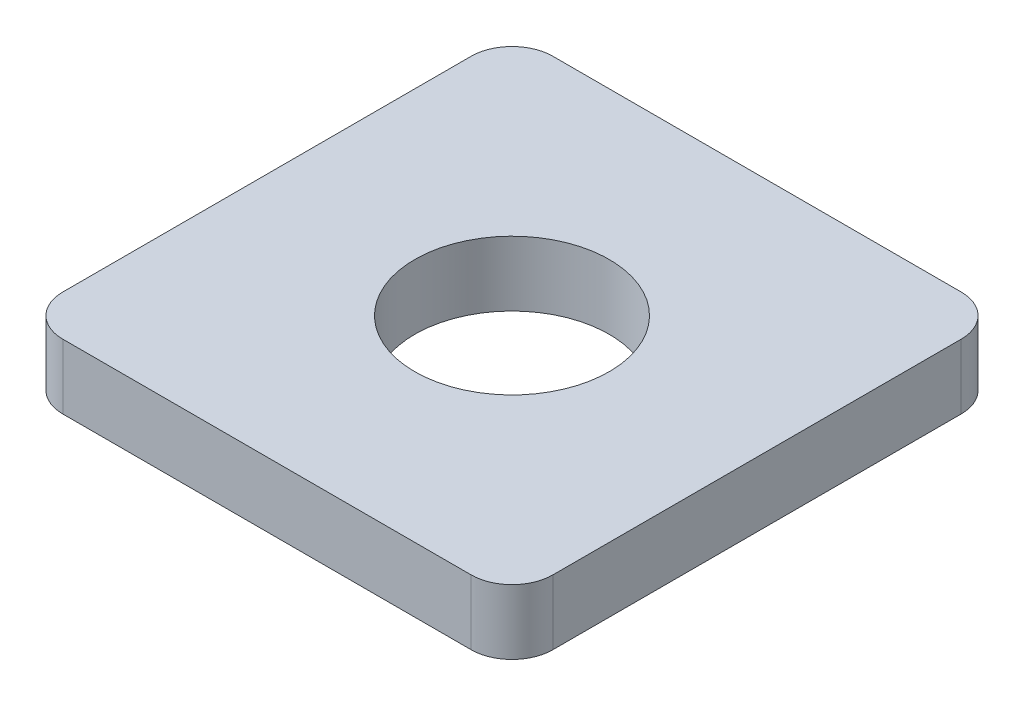
SolidWorks part; units mm, degrees
ref_plane "Front Plane" through (0, 0, 0) normal (0, 0, 1) x (1, 0, 0)
ref_plane "Top Plane" through (0, 0, 0) normal (0, 1, 0) x (1, 0, 0)
ref_plane "Right Plane" through (0, 0, 0) normal (1, 0, 0) x (0, 0, -1)
sketch "Sketch1" plane through (0, 0, 0) normal (0, 1, 0) x (1, 0, 0)
  line L0 (-6, -6) -> (6, 6) construction
  line L1 (-6, 6) -> (6, 6)
  line L2 (-6, 6) -> (-6, -6)
  line L3 (-6, -6) -> (6, -6)
  line L4 (6, 6) -> (6, -6)
  circle A0 centre (0, 0) radius 2.3813
  dimension "D1" = 4.7625
  dimension "D2" = 12
  dimension "D3" = 12
extrude "Boss-Extrude1" add sketch "Sketch1" along normal blind 1.5875
fillet "Fillet1" radius 1 4 edges at (-6, 0.7937, 6) (6, 0.7937, 6) (-6, 0.7937, -6) (6, 0.7937, -6)
